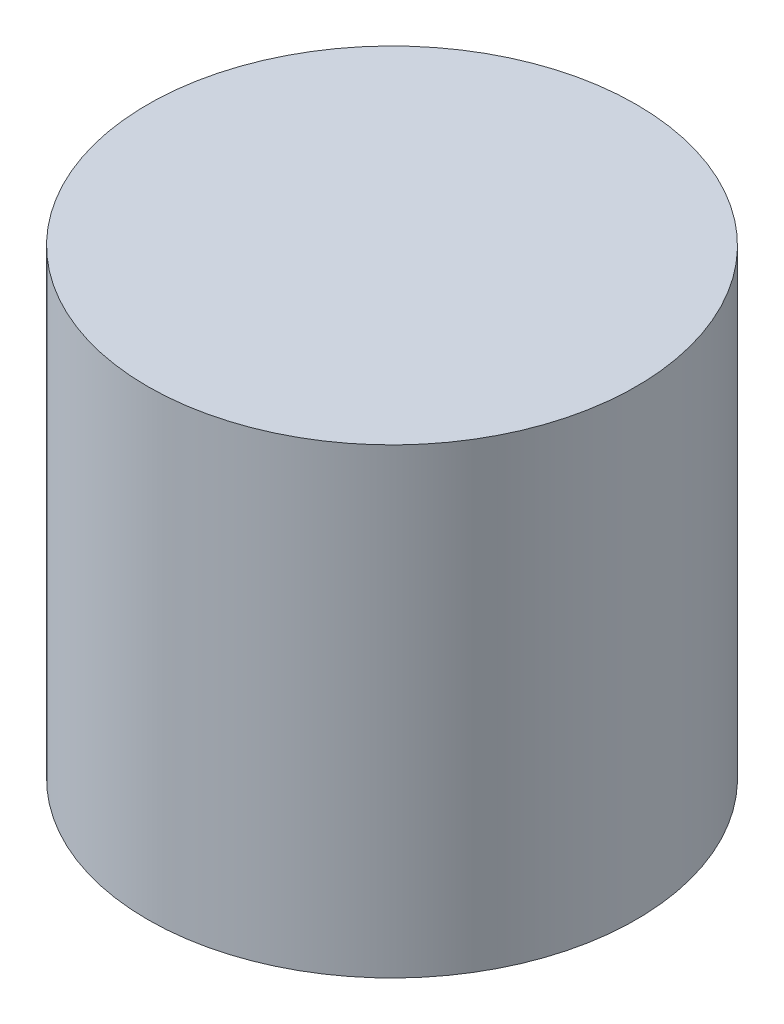
SolidWorks part; units mm, degrees
ref_plane "Front Plane" through (0, 0, 0) normal (0, 0, 1) x (1, 0, 0)
ref_plane "Top Plane" through (0, 0, 0) normal (0, 1, 0) x (1, 0, 0)
ref_plane "Right Plane" through (0, 0, 0) normal (1, 0, 0) x (0, 0, -1)
sketch "Sketch1" plane through (0, 0, 0) normal (0, 1, 0) x (1, 0, 0)
  circle A0 centre (0, 0) radius 15.875
  dimension "D1" = 31.75
extrude "Boss-Extrude1" add sketch "Sketch1" along normal blind 30
